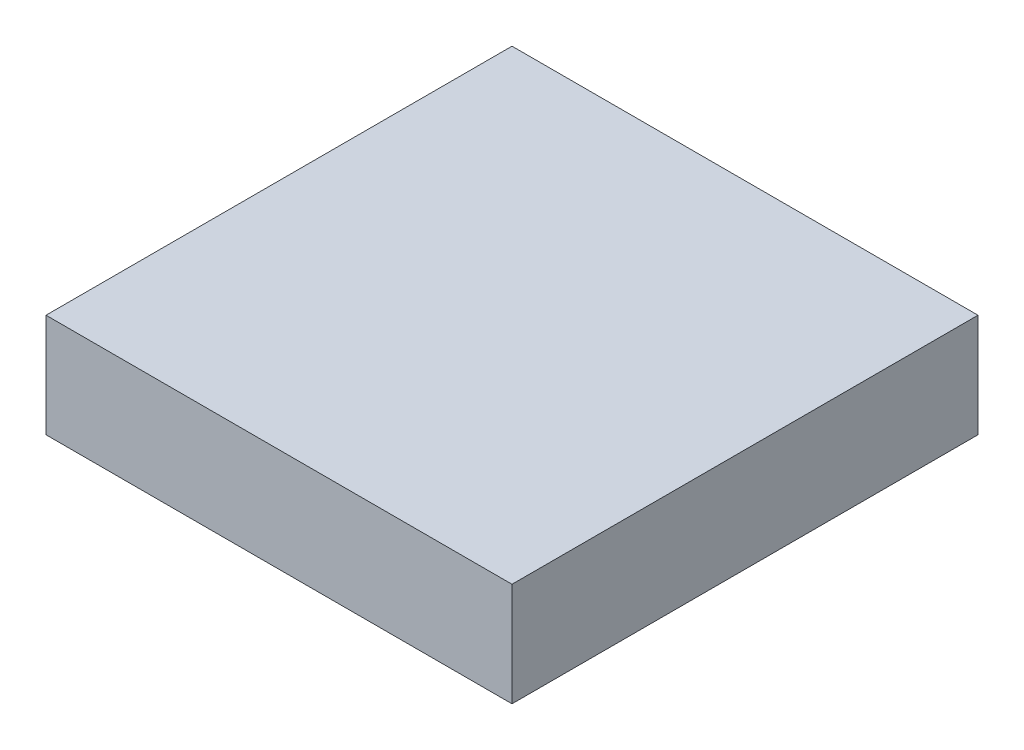
SolidWorks part; units mm, degrees
ref_plane "Front Plane" through (0, 0, 0) normal (0, 0, 1) x (1, 0, 0)
ref_plane "Top Plane" through (0, 0, 0) normal (0, 1, 0) x (1, 0, 0)
ref_plane "Right Plane" through (0, 0, 0) normal (1, 0, 0) x (0, 0, -1)
sketch "Sketch4" plane through (0, 0, 0) normal (0, 1, 0) x (1, 0, 0)
  line L1 (-22.5, 22.5) -> (22.5, 22.5)
  line L2 (-22.5, 22.5) -> (-22.5, -22.5)
  line L3 (-22.5, -22.5) -> (22.5, -22.5)
  line L4 (22.5, 22.5) -> (22.5, -22.5)
  line L5 (-22.5, 22.5) -> (22.5, -22.5) construction
  line L6 (-22.5, -22.5) -> (22.5, 22.5) construction
  point P0 (0, 0)
  dimension "D1" = 45
  dimension "D2" = 45
extrude "Boss-Extrude1" add sketch "Sketch4" along normal blind 10
